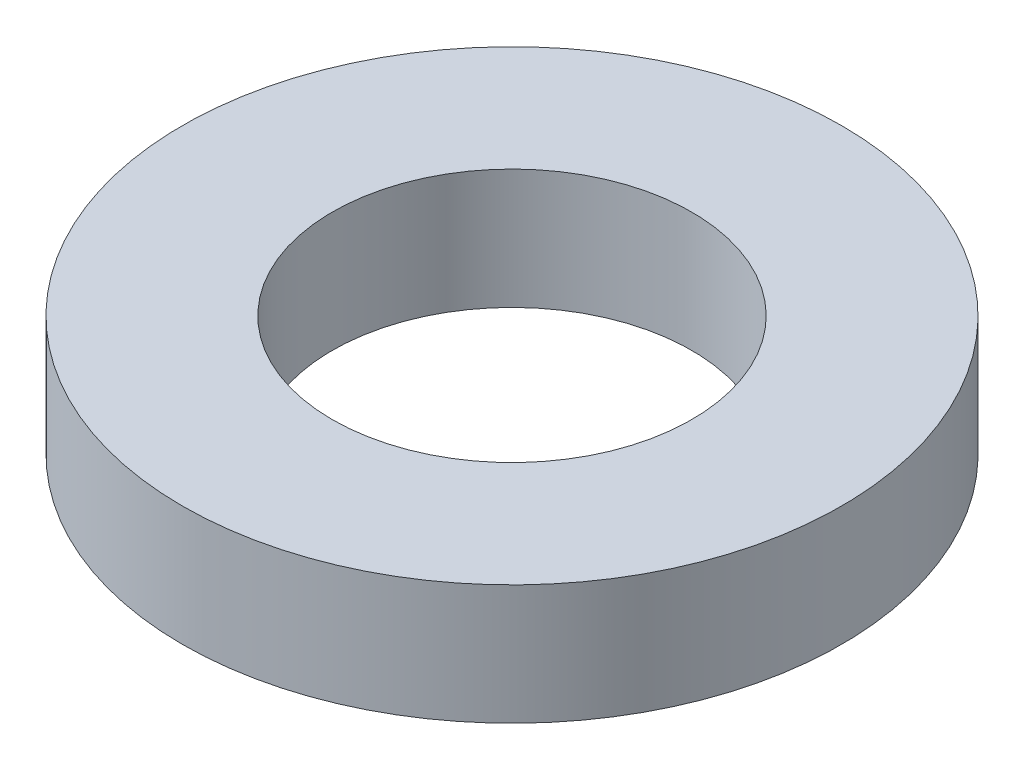
SolidWorks part; units mm, degrees
material "Plain Carbon Steel"
ref_plane "Front Plane" through (0, 0, 0) normal (0, 0, 1) x (1, 0, 0)
ref_plane "Top Plane" through (0, 0, 0) normal (0, 1, 0) x (1, 0, 0)
ref_plane "Right Plane" through (0, 0, 0) normal (1, 0, 0) x (0, 0, -1)
sketch "Sketch1" plane through (0, 0, 0) normal (0, 1, 0) x (1, 0, 0)
  circle A0 centre (0, 0) radius 1.5
  circle A1 centre (0, 0) radius 2.75
  dimension "D1" = 3
  dimension "D2" = 5.5
extrude "Boss-Extrude1" add sketch "Sketch1" along normal blind 1
